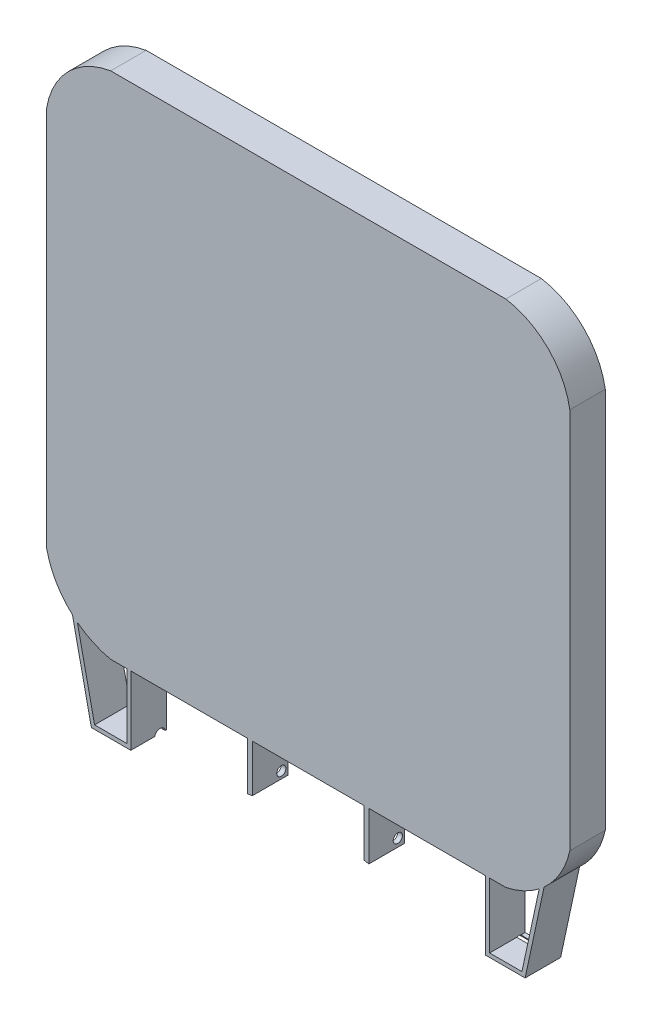
SolidWorks part; units mm, degrees
ref_plane "Front Plane" through (0, 0, 0) normal (0, 0, 1) x (1, 0, 0)
ref_plane "Top Plane" through (0, 0, 0) normal (0, 1, 0) x (1, 0, 0)
ref_plane "Right Plane" through (0, 0, 0) normal (1, 0, 0) x (0, 0, -1)
sketch "Sketch1" plane through (0, 0, 0) normal (0, 0, 1) x (1, 0, 0)
  line L8 (-199, 125.1452) -> (-199, -165.4239)
  line L9 (-150.432, -213.9597) -> (150.432, -213.9597)
  line L10 (199, -165.4239) -> (199, 125.1452)
  line L11 (150.3335, 173.7795) -> (-150.3335, 173.7795)
  line L16 (-195, 124.8104) -> (-195, -164.9906)
  line L17 (-150, -209.9597) -> (150, -209.9597)
  line L18 (195, -164.9906) -> (195, 124.8104)
  line L19 (150, 169.7795) -> (-150, 169.7795)
  line L20 (-195, 124.8104) -> (-195, -164.9906)
  line L21 (-150, -209.9597) -> (150, -209.9597)
  line L22 (195, -164.9906) -> (195, 124.8104)
  line L23 (150, 169.7795) -> (-150, 169.7795)
  arc A8 (-199, -165.4239) -> (-150.432, -213.9597) centre (-137.1349, -152.0857) ccw
  arc A9 (150.432, -213.9597) -> (199, -165.4239) centre (137.1349, -152.0857) ccw
  arc A10 (199, 125.1452) -> (150.3335, 173.7795) centre (140.718, 115.491) ccw
  arc A11 (-150.3335, 173.7795) -> (-199, 125.1452) centre (-140.718, 115.491) ccw
  arc A24 (-150, 169.7795) -> (-195, 124.8104) centre (-140.718, 115.491) ccw construction
  arc A25 (-195, -164.9906) -> (-150, -209.9597) centre (-137.1349, -152.0857) ccw construction
  arc A26 (150, -209.9597) -> (195, -164.9906) centre (137.1349, -152.0857) ccw construction
  arc A27 (195, 124.8104) -> (150, 169.7795) centre (140.718, 115.491) ccw construction
  ellipse E12 centre (-150, 124.8104) end of major axis (-105, 124.8104) minor radius 44.9691 (-150, 169.7795) -> (-195, 124.8104) ccw
  ellipse E13 centre (-150, 124.8104) end of major axis (-105, 124.8104) minor radius 44.9691 (-150, 169.7795) -> (-195, 124.8104) ccw
  ellipse E14 centre (-150, -164.9906) end of major axis (-105, -164.9906) minor radius 44.9691 (-195, -164.9906) -> (-150, -209.9597) ccw
  ellipse E15 centre (-150, -164.9906) end of major axis (-105, -164.9906) minor radius 44.9691 (-195, -164.9906) -> (-150, -209.9597) ccw
  ellipse E16 centre (150, -164.9906) end of major axis (195, -164.9906) minor radius 44.9691 (150, -209.9597) -> (195, -164.9906) ccw
  ellipse E17 centre (150, -164.9906) end of major axis (195, -164.9906) minor radius 44.9691 (150, -209.9597) -> (195, -164.9906) ccw
  ellipse E18 centre (150, 124.8104) end of major axis (105, 124.8104) minor radius 44.9691 (195, 124.8104) -> (150, 169.7795) ccw
  ellipse E19 centre (150, 124.8104) end of major axis (105, 124.8104) minor radius 44.9691 (195, 124.8104) -> (150, 169.7795) ccw
  dimension "D1" = 0
  dimension "D2" = 4
  dimension "D3" = 290.5692
extrude "Boss-Extrude1" add sketch "Sketch1" along normal blind 25
sketch "Sketch2" plane through (0, 0, 25) normal (0, 0, 1) x (1, 0, 0)
  line L4 (-199, 125.1452) -> (-199, -165.4239)
  line L5 (-150.432, -213.9597) -> (150.432, -213.9597)
  line L6 (199, -165.4239) -> (199, 125.1452)
  line L7 (150.3335, 173.7795) -> (-150.3335, 173.7795)
  line L12 (-199, 125.1452) -> (-199, -165.4239)
  line L13 (-150.432, -213.9597) -> (150.432, -213.9597)
  line L14 (199, -165.4239) -> (199, 125.1452)
  line L15 (150.3335, 173.7795) -> (-150.3335, 173.7795)
  arc A5 (-150.3335, 173.7795) -> (-199, 125.1452) centre (-140.718, 115.491) ccw
  arc A6 (-199, -165.4239) -> (-150.432, -213.9597) centre (-137.1349, -152.0857) ccw
  arc A7 (150.432, -213.9597) -> (199, -165.4239) centre (137.1349, -152.0857) ccw
  arc A12 (199, 125.1452) -> (150.3335, 173.7795) centre (140.718, 115.491) ccw
  arc A13 (-150.3335, 173.7795) -> (-199, 125.1452) centre (-140.718, 115.491) ccw
  arc A14 (-199, -165.4239) -> (-150.432, -213.9597) centre (-137.1349, -152.0857) ccw
  arc A15 (150.432, -213.9597) -> (199, -165.4239) centre (137.1349, -152.0857) ccw
  arc A16 (199, 125.1452) -> (150.3335, 173.7795) centre (140.718, 115.491) ccw
  dimension "D1" = 0
extrude "Boss-Extrude2" add sketch "Sketch2" along normal blind 2
sketch "Sketch3" plane through (0, 0, 27) normal (0, 0, 1) x (1, 0, 0)
  line L0 (-135, -204) -> (-135, -266.2988)
  line L2 (-135, -266.2988) -> (-165, -266.2988)
  line L3 (-165, -266.2988) -> (-180.6885, -193.2567)
  line L4 (-135, -204) -> (-138, -204)
  line L7 (-162.5759, -263.2988) -> (-177.0517, -195.9029)
  line L10 (-138, -204) -> (-138, -263.2988)
  line L11 (-138, -263.2988) -> (-162.5759, -263.2988)
  line L12 (-180.6885, -193.2567) -> (-181.0133, -190.8884)
  line L13 (-181.0133, -190.8884) -> (-177.0517, -193.8943)
  line L14 (-177.0517, -193.8943) -> (-177.0517, -195.9029)
  dimension "D1" = 30
extrude "Boss-Extrude3" add sketch "Sketch3" against normal up to surface (27 mm away) up to face at (0, -19.9506, 0)
mirror "Mirror1" about plane through (0, 0, 0) normal (1, 0, 0) of "Boss-Extrude3"
sketch "Sketch4" plane through (-135, 0, 0) normal (1, 0, 0) x (0, 0, -1)
  circle A0 centre (-4.7902, -266.9686) radius 4
extrude "Cut-Extrude1" cut sketch "Sketch4" against normal blind 10 and the other way blind 290
sketch "Sketch5" plane through (0, 0, 27) normal (0, 0, 1) x (1, 0, 0)
  line L0 (0, 173.7795) -> (0, -273.8986) construction
  line L1 (150.3335, 173.7795) -> (-150.3335, 173.7795) construction
  line L2 (-46.1305, -213.9597) -> (-46.1305, -250.5806)
  line L3 (-135, -213.9597) -> (135, -213.9597) construction
  line L4 (-46.1305, -250.5806) -> (-42.5, -249.9435)
  line L5 (-42.5, -249.9435) -> (-42.5, -213.9597)
  line L6 (-42.5, -213.9597) -> (-46.1305, -213.9597)
  line L7 (46.1305, -250.5806) -> (42.5, -249.9435)
  line L8 (42.5, -213.9597) -> (46.1305, -213.9597)
  line L9 (42.5, -249.9435) -> (42.5, -213.9597)
  line L10 (46.1305, -213.9597) -> (46.1305, -250.5806)
  dimension "D1" = 410
  dimension "D2" = 42.5
extrude "Boss-Extrude4" add sketch "Sketch5" against normal up to surface (27 mm away) up to face at (153.068, -231.64, 0)
sketch "Sketch6" plane through (46.1305, 0, 0) normal (1, 0, 0) x (0, 0, -1)
  line L0 (0, -250.5806) -> (-27, -250.5806) construction
  line L1 (0, -213.9597) -> (0, -250.5806) construction
  circle A0 centre (-5, -244.5806) radius 3.5
  dimension "D1" = 7
  dimension "D2" = 6
  dimension "D3" = 5
extrude "Cut-Extrude2" cut sketch "Sketch6" against normal blind 108
